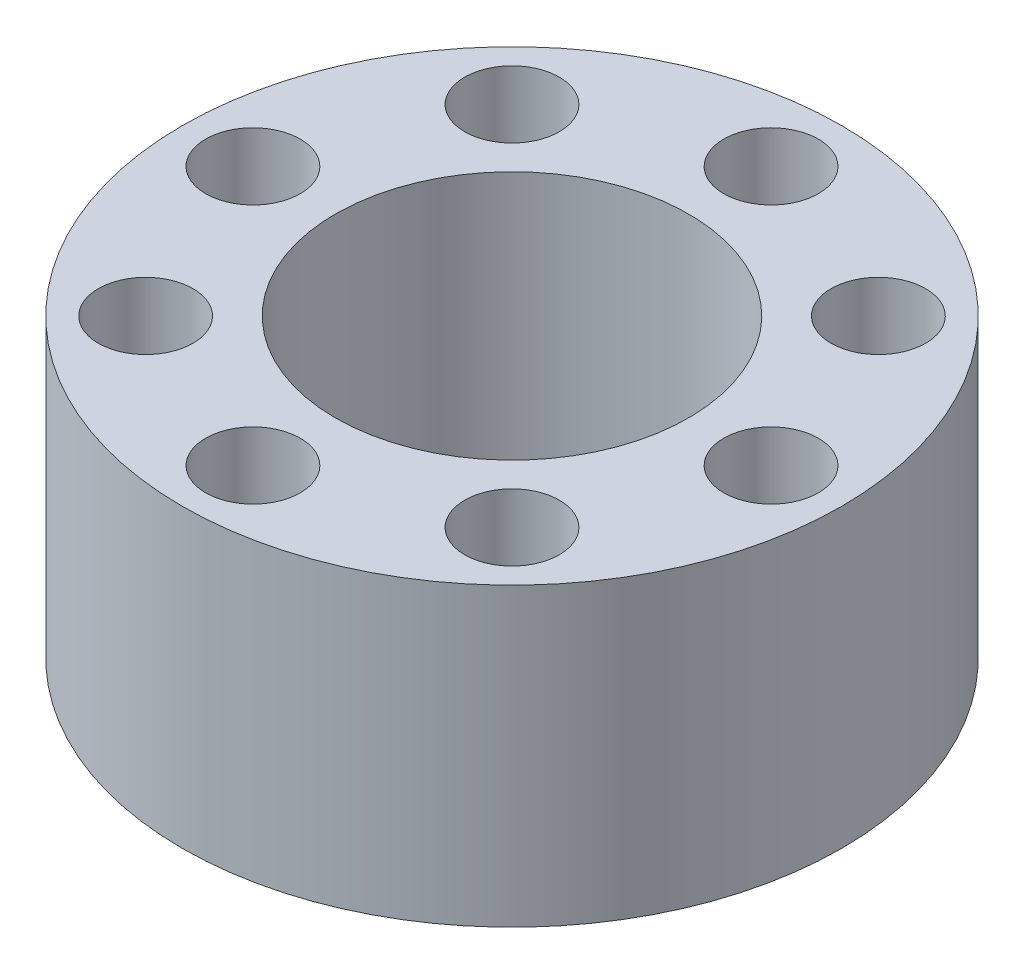
SolidWorks part; units mm, degrees
material "Acrylic (Medium-high impact)"
ref_plane "Front" through (0, 0, 0) normal (0, 0, 1) x (1, 0, 0)
ref_plane "Top" through (0, 0, 0) normal (0, 1, 0) x (1, 0, 0)
ref_plane "Right" through (0, 0, 0) normal (1, 0, 0) x (0, 0, -1)
sketch "Sketch1" plane through (0, 0, 0) normal (0, 1, 0) x (1, 0, 0)
  circle A0 centre (0, 0) radius 17.78
  circle A1 centre (0, 13.97) radius 2.5527
  circle A2 centre (9.8783, 9.8783) radius 2.5527
  circle A3 centre (13.97, 0) radius 2.5527
  circle A4 centre (9.8783, -9.8783) radius 2.5527
  circle A5 centre (0, -13.97) radius 2.5527
  circle A6 centre (-9.8783, -9.8783) radius 2.5527
  circle A7 centre (-13.97, 0) radius 2.5527
  circle A8 centre (-9.8783, 9.8783) radius 2.5527
  circle A9 centre (0, 0) radius 9.525
  point P21 (0, 0)
  dimension "D1" = 35.56
  dimension "D2" = 5.1054
  dimension "D5" = 19.05
  dimension "D3" = 13.97
  dimension "D4" = 8
extrude "Boss-Extrude1" add sketch "Sketch1" along normal blind 15.9766
